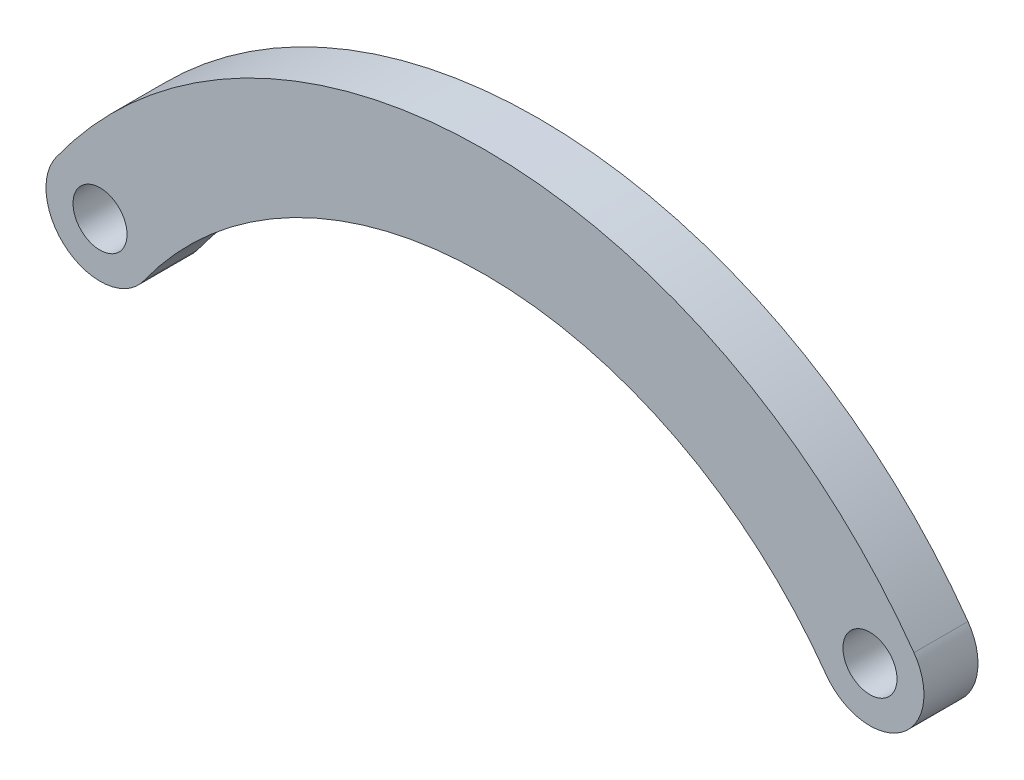
SolidWorks part; units mm, degrees
material "Thornel Mat VMA"
ref_plane "前视基准面" through (0, 0, 0) normal (0, 0, 1) x (1, 0, 0)
ref_plane "上视基准面" through (0, 0, 0) normal (0, 1, 0) x (1, 0, 0)
ref_plane "右视基准面" through (0, 0, 0) normal (1, 0, 0) x (0, 0, -1)
sketch "草图1" plane through (0, 0, 0) normal (0, 0, 1) x (1, 0, 0)
  line L0 (-28.5, 0) -> (28.5, 0) construction
  circle A0 centre (28.5, 0) radius 2
  circle A1 centre (-28.5, 0) radius 2
  arc A2 (-28.5, 0) -> (28.5, 0) centre (0, -20.3162) cw construction
  arc A3 (-25.2429, -2.3219) -> (25.2429, -2.3219) centre (0, -20.3162) cw
  arc A4 (-31.7571, 2.3219) -> (31.7571, 2.3219) centre (0, -20.3162) cw
  arc A5 (-25.2429, -2.3219) -> (-31.7571, 2.3219) centre (-28.5, 0) cw
  arc A6 (25.2429, -2.3219) -> (31.7571, 2.3219) centre (28.5, 0) ccw
  point P4 (0, 0)
  dimension "D2" = 35
  dimension "D3" = 4
  dimension "D1" = 57
  dimension "D4" = 4
  dimension "D5" = 4
extrude "凸台-拉伸1" add sketch "草图1" along normal mid plane 4
